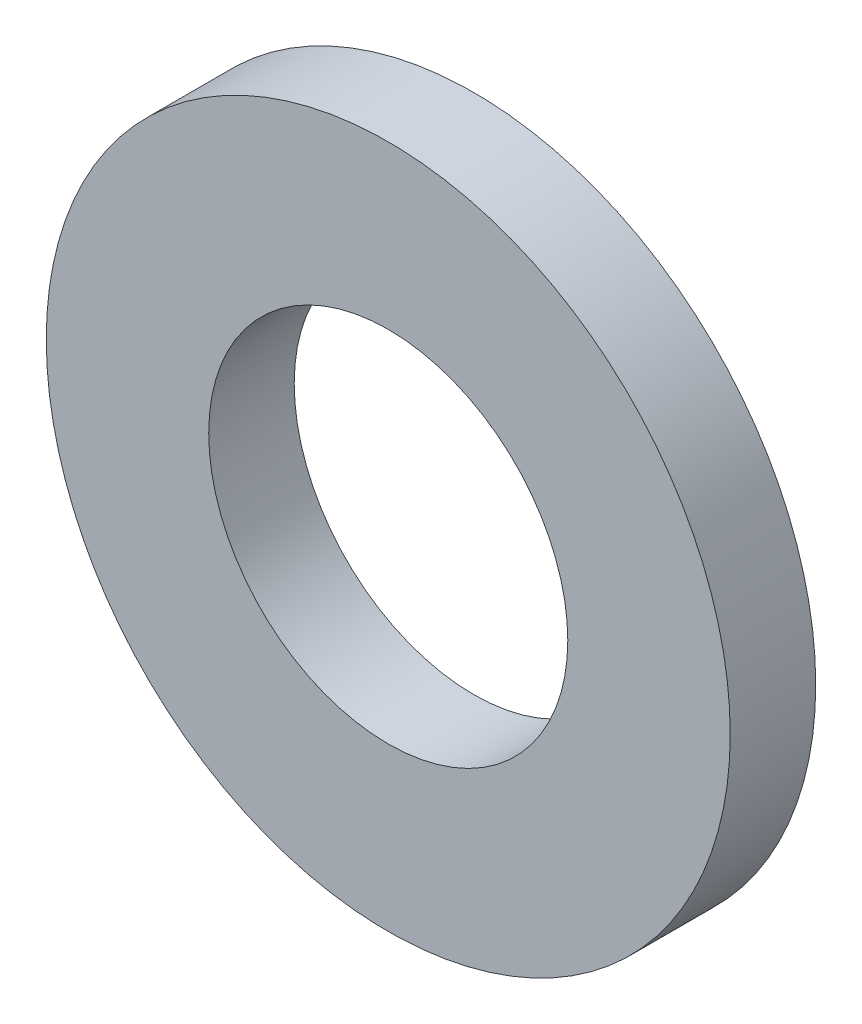
SolidWorks part; units mm, degrees
material "PC High Viscosity"
ref_plane "Front Plane" through (0, 0, 0) normal (0, 0, 1) x (1, 0, 0)
ref_plane "Top Plane" through (0, 0, 0) normal (0, 1, 0) x (1, 0, 0)
ref_plane "Right Plane" through (0, 0, 0) normal (1, 0, 0) x (0, 0, -1)
sketch "Sketch1" plane through (0, 0, 0) normal (0, 0, 1) x (1, 0, 0)
  circle A0 centre (0, 0) radius 2 construction
  circle A1 centre (0, 0) radius 1.05 construction
  point P5 (-1.05, 0)
  point P6 (1.05, 0)
  point P7 (2, 0)
  point P8 (-2, 0)
  point P9 (0, 0)
  point P10 (0, -1.05)
  dimension "OD" = 4
  dimension "ID" = 2.1
sketch "Sketch2" plane through (0, 0, 0) normal (1, 0, 0) x (0, 0, -1)
  line L0 (0, 2) -> (0, -2) construction
  line L1 (0, 2) -> (0, -2) construction
  line L2 (-0.25, 2) -> (0.25, 2) construction
  line L3 (-0.25, 0) -> (0.25, 0) construction
  line L4 (-0.25, -2) -> (0.25, -2) construction
  line L5 (0.25, -2) -> (0.25, 2) construction
  line L6 (-0.25, -2) -> (-0.25, 2) construction
  point P5 (0, 2)
  point P8 (0, 0)
  point P11 (0, -2)
  point P12 (0.25, 2)
  point P13 (0.25, 0)
  point P14 (0.25, -2)
  point P15 (-0.25, -2)
  point P16 (-0.25, 0)
  point P17 (-0.25, 2)
  dimension "Thickness Range" = 0.5
sketch "Sketch3" plane through (0, 0, 0) normal (0, 0, 1) x (1, 0, 0)
  circle A0 centre (0, 0) radius 2 construction
  circle A1 centre (0, 0) radius 1.05 construction
  circle A2 centre (0, 0) radius 2
  circle A3 centre (0, 0) radius 1.05
extrude "Boss-Extrude1" add sketch "Sketch3" along normal mid plane 0.5
equation "\"D1@Boss-Extrude1\" = \"Thickness Range@Sketch2\""
